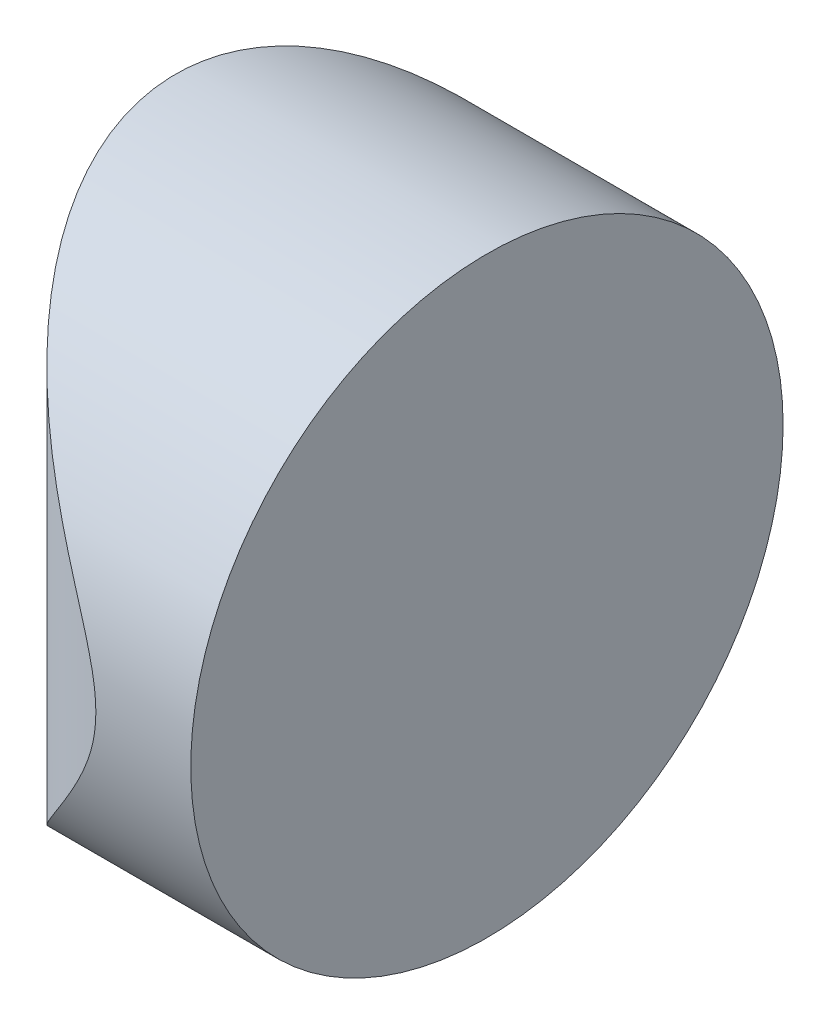
SolidWorks part; units mm, degrees
ref_plane "前视基准面" through (0, 0, 0) normal (0, 0, 1) x (1, 0, 0)
ref_plane "上视基准面" through (0, 0, 0) normal (0, 1, 0) x (1, 0, 0)
ref_plane "右视基准面" through (0, 0, 0) normal (1, 0, 0) x (0, 0, -1)
sketch "草图1" plane through (0, 0, 0) normal (0, 1, 0) x (1, 0, 0)
  line L0 (10.7432, 0) -> (-19.1624, 0) construction
  line L1 (2.3624, 6.25) -> (4.3652, 6.25)
  line L2 (2.3624, -6.25) -> (4.3652, -6.25)
  line L3 (4.3652, 6.25) -> (4.3652, -6.25)
  arc A0 (2.3624, 6.25) -> (2.3624, -6.25) centre (4.3552, 0) ccw
  point P19 (-2.2048, 0)
  point P20 (4.3652, 0)
  dimension "D2" = 6.25
  dimension "D3" = 6.56
  dimension "D4" = 6.57
  dimension "D1" = 6.25
extrude "凸台-拉伸1" add sketch "草图1" along normal blind 12.5 contours A0 L2 L3 L1
sketch "草图2" plane through (4.3652, 0, 0) normal (1, 0, 0) x (0, 0, -1)
  line L0 (6.25, 0) -> (-6.25, 0) construction
  line L7 (-6.25, 0) -> (6.25, 0)
  line L8 (6.25, 0) -> (6.25, 12.5)
  line L9 (6.25, 12.5) -> (-6.25, 12.5)
  line L10 (-6.25, 12.5) -> (-6.25, 0)
  line L11 (-6.25, 0) -> (6.25, 0)
  line L12 (6.25, 0) -> (6.25, 12.5)
  line L13 (6.25, 12.5) -> (-6.25, 12.5)
  line L14 (-6.25, 12.5) -> (-6.25, 0)
  circle A0 centre (0, 6.25) radius 6.25
  point P2 (0, 0)
  point P7 (-0.5623, 8.5488)
  line M1 (-6.25, 0) -> (6.25, 0)
  line M2 (6.25, 0) -> (6.25, 12.5)
  line M3 (6.25, 12.5) -> (-6.25, 12.5)
  line M4 (-6.25, 12.5) -> (-6.25, 0)
  dimension "D1" = 12.5
  dimension "D2" = 6.25
  dimension "D3" = 0
extrude "切除-拉伸8" cut sketch "草图2" against normal blind 12.7 contours A0 L13 M4 | A0 L12 M3 | A0 L11 M2 | A0 L14 M1
